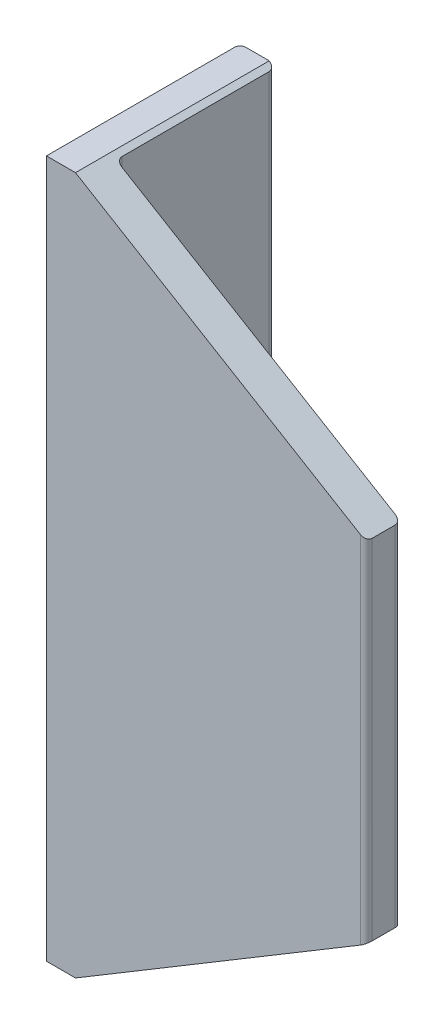
SolidWorks part; units mm, degrees
ref_plane "Front Plane" through (0, 0, 0) normal (0, 0, 1) x (1, 0, 0)
ref_plane "Top Plane" through (0, 0, 0) normal (0, 1, 0) x (1, 0, 0)
ref_plane "Right Plane" through (0, 0, 0) normal (1, 0, 0) x (0, 0, -1)
sketch "Sketch1" plane through (0, 0, 0) normal (0, 1, 0) x (1, 0, 0)
  line L0 (0, 0) -> (0, 32.3333)
  line L1 (1, 33.3333) -> (5, 33.3333)
  line L2 (6, 32.3333) -> (6, 7)
  line L3 (7, 6) -> (54, 6)
  line L4 (55, 5) -> (55, 1)
  line L5 (54, 0) -> (0, 0)
  arc A0 (55, 1) -> (54, 0) centre (54, 1) cw
  arc A1 (54, 6) -> (55, 5) centre (54, 5) cw
  arc A2 (6, 7) -> (7, 6) centre (7, 7) ccw
  arc A3 (5, 33.3333) -> (6, 32.3333) centre (5, 32.3333) cw
  arc A4 (0, 32.3333) -> (1, 33.3333) centre (1, 32.3333) cw
  point P9 (55, 0)
  point P12 (55, 6)
  point P17 (6, 33.3333)
  point P20 (0, 33.3333)
  dimension "D5" = 1
  dimension "D1" = 55
  dimension "D2" = 33.3333
  dimension "D3" = 6
  dimension "D4" = 6
extrude "Boss-Extrude1" add sketch "Sketch1" along normal blind 120
ref_plane "Plane1" through (0, 60, 0) normal (0, 1, 0) x (1, 0, 0)
sketch "Sketch4" plane through (0, 60, 0) normal (0, 1, 0) x (1, 0, 0)
  line L0 (6, 32.3333) -> (54, 6)
rib "Rib6" sketch "Sketch4" sketch "Sketch4" thickness 6 extrusion direction parallel to sketch draft on no parameters "D1"=6
sketch "Sketch5" plane through (0, 0, 0) normal (0, 0, 1) x (1, 0, 0)
  line L0 (55, 120) -> (5, 120)
  line L1 (0, 120) -> (54, 120) construction
  line L2 (5, 120) -> (55, 90)
  line L3 (55, 120) -> (55, 0) construction
  line L4 (55, 90) -> (55, 120)
  line L5 (-18.4643, 60) -> (129.2396, 60) construction
  line L6 (61.875, 60) -> (-61.875, 60) construction
  line L7 (55, 30) -> (55, 0)
  line L8 (5, 0) -> (55, 30)
  line L9 (55, 0) -> (5, 0)
  dimension "D1" = 50
  dimension "D2" = 30
extrude "Cut-Extrude1" cut sketch "Sketch5" against normal through all
scale "Scale3" scale about centroid uniform scaling yes scale factor 7.5
